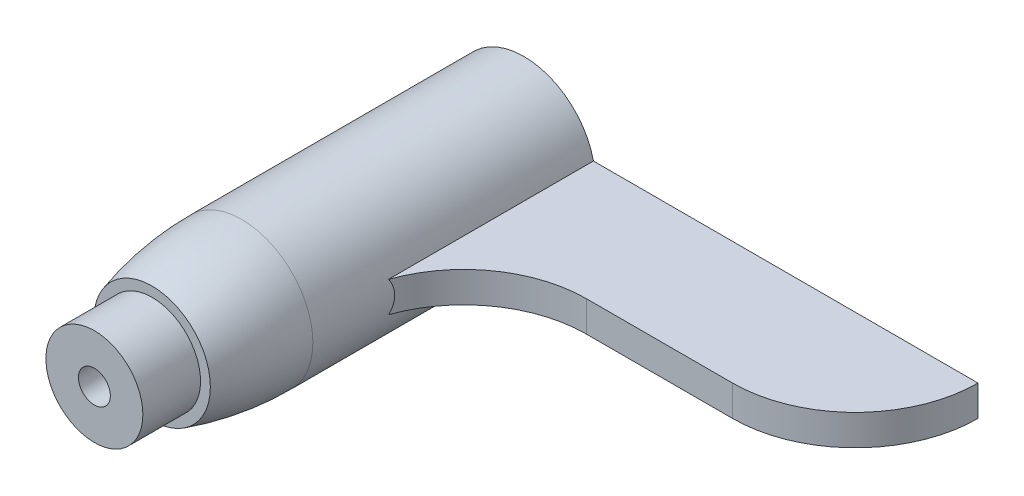
SolidWorks part; units mm, degrees
ref_plane "Front Plane" through (0, 0, 0) normal (0, 0, 1) x (1, 0, 0)
ref_plane "Top Plane" through (0, 0, 0) normal (0, 1, 0) x (1, 0, 0)
ref_plane "Right Plane" through (0, 0, 0) normal (1, 0, 0) x (0, 0, -1)
sketch "Sketch1" plane through (0, 0, 0) normal (0, 0, 1) x (1, 0, 0)
  circle A0 centre (0, 0) radius 5.8
  dimension "D1" = 11.6
extrude "Boss-Extrude1" add sketch "Sketch1" along normal blind 23
sketch "Sketch2" plane through (0, 0, 0) normal (0, 1, 0) x (1, 0, 0)
  line L0 (0, 0) -> (37, 0)
  line L1 (27, -10) -> (15.1015, -10)
  line L2 (5.1015, -20) -> (0, -20)
  line L3 (0, -20) -> (0, 0)
  line L4 (5.8, -23) -> (5.8, 0) construction
  arc A0 (37, 0) -> (27, -10) centre (27, 0) cw
  arc A1 (15.1015, -10) -> (5.1015, -20) centre (15.1015, -20) ccw
  dimension "D1" = 37
  dimension "D2" = 10
  dimension "D3" = 0.6985
extrude "Boss-Extrude2" add sketch "Sketch2" along normal mid plane 2.5
sketch "Sketch3" plane through (0, 0, 0) normal (0, 1, 0) x (1, 0, 0)
  line L0 (0, -1000) -> (0, 49000) construction
  line L1 (0, -23) -> (-5.8, -23)
  line L2 (-5.8, -23) -> (5.8, -23) construction
  line L3 (-3.95, -30.3) -> (-3.95, -35)
  line L4 (-3.95, -35) -> (0, -35)
  line L5 (0, -35) -> (0, -23)
  line L6 (-3.95, -30.3) -> (-4.75, -30.3)
  arc A0 (-5.8, -23) -> (-4.75, -30.3) centre (20.1012, -23) ccw
  dimension "D1" = 7.9
  dimension "D2" = 4.7
  dimension "D4" = 0.8
  dimension "D3" = 12
revolve "Revolve1" add sketch "Sketch3" angle 360 about L0
sketch "Sketch4" plane through (0, 0, 35) normal (0, 0, 1) x (1, 0, 0)
  circle A0 centre (0, 0) radius 1.3
  dimension "D1" = 2.6
extrude "Cut-Extrude1" cut sketch "Sketch4" against normal through all
